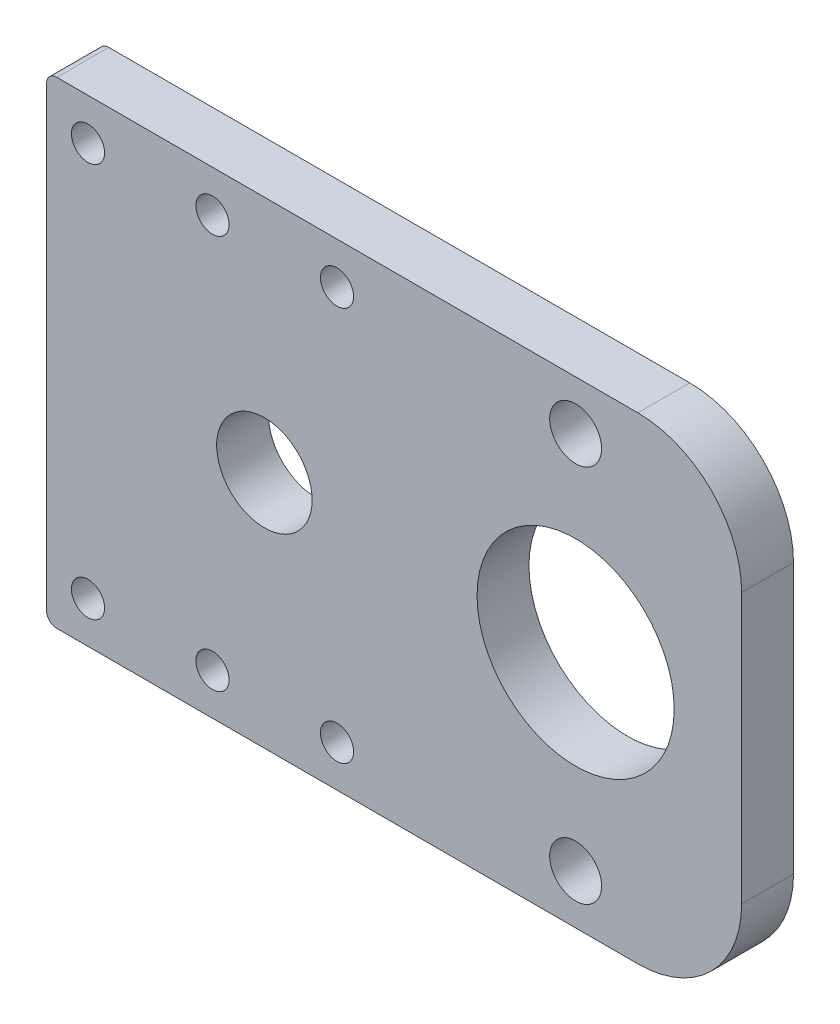
SolidWorks part; units mm, degrees
material "Acrylic (Medium-high impact)"
ref_plane "Front Plane" through (0, 0, 0) normal (0, 0, 1) x (1, 0, 0)
ref_plane "Top Plane" through (0, 0, 0) normal (0, 1, 0) x (1, 0, 0)
ref_plane "Right Plane" through (0, 0, 0) normal (1, 0, 0) x (0, 0, -1)
sketch "Sketch1" plane through (0, 0, 0) normal (0, 0, 1) x (1, 0, 0)
  line L0 (-25.3491, 0) -> (24.7222, 0) construction
  line L1 (40, -23) -> (-40, -23)
  line L2 (40, -23) -> (40, 23)
  line L3 (40, 23) -> (-40, 23)
  line L4 (-40, -23) -> (-40, 23)
  line L5 (40, -23) -> (-40, 23) construction
  line L6 (40, 23) -> (-40, -23) construction
  line L7 (30, 0) -> (30, 18.25)
  line L8 (-40, 23) -> (-25, 23)
  line L9 (-25, 23) -> (-25, -23)
  circle A0 centre (0, 0) radius 4.6
  circle A1 centre (30, 0) radius 9.5
  circle A2 centre (30, 18.25) radius 2.5
  circle A3 centre (30, -18.25) radius 2.5
  point P0 (0, 0)
  dimension "D1" = 9.2
  dimension "D2" = 19
  dimension "D7" = 5
  dimension "D3" = 46
  dimension "D4" = 30
  dimension "D5" = 80
  dimension "D6" = 18.25
  dimension "D8" = 15
extrude "Boss-Extrude1" add sketch "Sketch1" along normal blind 5
sketch "Sketch2" plane through (0, 0, 5) normal (0, 0, 1) x (1, 0, 0)
  line L0 (-25, -23) -> (-25, 23)
  line L1 (-25, -23) -> (-5, -23)
  line L2 (-25, 23) -> (-5, 23)
  line L3 (-5, -23) -> (-5, 23)
  line L4 (-25, 23) -> (-25, -23)
  line L5 (-25, -23) -> (40, -23)
  line L6 (40, -23) -> (40, 23)
  line L7 (40, 23) -> (-25, 23)
  line L9 (-25, -23) -> (40, -23)
  line L10 (40, -23) -> (40, 23)
  line L11 (40, 23) -> (-25, 23)
  line L12 (-17, 19) -> (-25, 19)
  line L13 (-17, 19) -> (-5, 19)
  line L14 (-5, 19) -> (7, 19)
  line L16 (-5, 0) -> (-25, 0)
  line L20 (-25, 23) -> (-25, -23)
  circle A0 centre (-17, 19) radius 1.6
  circle A1 centre (-5, 19) radius 1.6
  circle A5 centre (7, 19) radius 1.6
  circle A6 centre (7, -19) radius 1.6
  circle A7 centre (-5, -19) radius 1.6
  circle A8 centre (-17, -19) radius 1.6
  dimension "D5" = 3.2
  dimension "D6" = 3.2
  dimension "D7" = 19
  dimension "D8" = 3.2
  dimension "D2" = 20
  dimension "D3" = 12
  dimension "D4" = 12
  dimension "D9" = 8
  dimension "D1" = 0
extrude "Cut-Extrude1" cut sketch "Sketch2" against normal blind 10
sketch "Sketch3" plane through (0, 0, 5) normal (0, 0, 1) x (1, 0, 0)
  line L0 (-25, 23) -> (-21, 23)
  line L1 (-21, 23) -> (-21, -23)
  line L4 (40, 23) -> (-25, 23)
  line L5 (-25, 23) -> (-25, -23)
  line L6 (-25, -23) -> (40, -23)
  line L7 (40, -23) -> (40, 23)
  line L8 (40, 23) -> (-25, 23)
  line L9 (-25, 23) -> (-25, -23)
  line L10 (-25, -23) -> (40, -23)
  line L11 (40, -23) -> (40, 23)
  line M10 (40, 23) -> (-25, 23)
  line M11 (-25, 23) -> (-25, -23)
  line M12 (-25, -23) -> (40, -23)
  dimension "D2" = 4
  dimension "D1" = 0
extrude "Cut-Extrude2" cut sketch "Sketch3" against normal through all contours L1 M10 M11 M12
sketch "Sketch4" plane through (0, 0, 5) normal (0, 0, 1) x (1, 0, 0)
  line L1 (40, 23) -> (46, 23)
  line L2 (40, 23) -> (40, -23)
  line L3 (40, -23) -> (46, -23)
  line L4 (40, 23) -> (-21, 23)
  line L5 (-21, 23) -> (-21, -23)
  line L6 (-21, -23) -> (40, -23)
  line L7 (40, -23) -> (40, 23)
  line L8 (40, 23) -> (-21, 23)
  line L9 (-21, 23) -> (-21, -23)
  line L10 (-21, -23) -> (40, -23)
  line L11 (40, -23) -> (40, 23)
  line L12 (46, 23) -> (46, -23)
  line M19 (40, -23) -> (40, 23)
  dimension "D2" = 6
  dimension "D1" = 0
extrude "Boss-Extrude2" add sketch "Sketch4" against normal up to surface (5 mm away) contours L12 L1 L3 M19 up to face at (-15.4, 19, 0)
fillet "Fillet1" radius 10 2 edges at (46, 23, 2.5) (46, -23, 2.5)
fillet "Fillet2" radius 1 2 edges at (-21, 23, 2.5) (-21, -23, 2.5)
